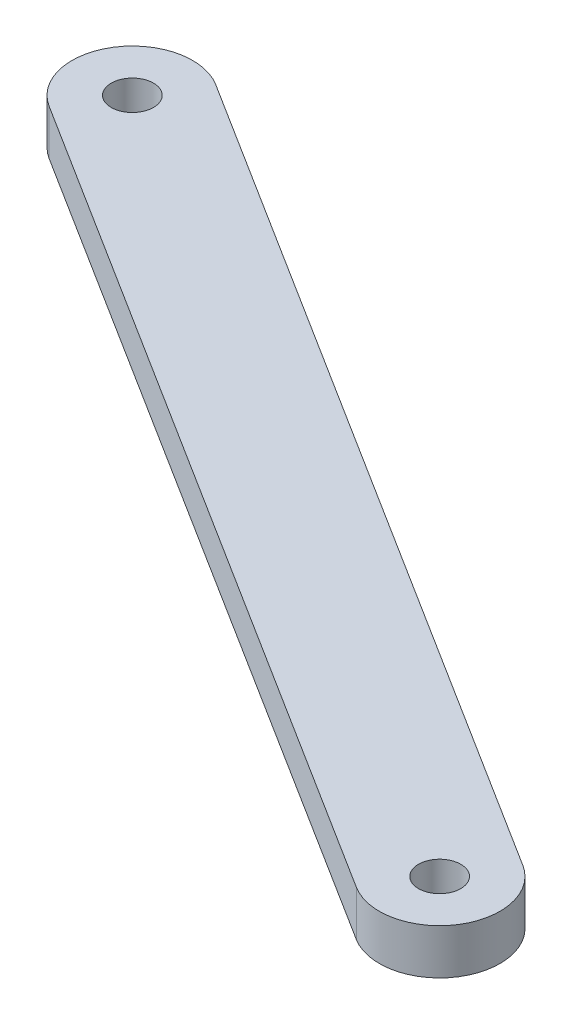
SolidWorks part; units mm, degrees
ref_plane "Front Plane" through (0, 0, 0) normal (0, 0, 1) x (1, 0, 0)
ref_plane "Top Plane" through (0, 0, 0) normal (0, 1, 0) x (1, 0, 0)
ref_plane "Right Plane" through (0, 0, 0) normal (1, 0, 0) x (0, 0, -1)
sketch "Sketch1" plane through (0, 0, 0) normal (0, 1, 0) x (1, 0, 0)
  line L20 (-2.1322, -19.4967) -> (-57.1322, 15.1443)
  line L25 (-61.3957, 8.3751) -> (-6.3957, -26.266)
  circle A59 centre (-4.2639, -22.8813) radius 1.4
  arc A60 (-57.1322, 15.1443) -> (-61.3957, 8.3751) centre (-59.2639, 11.7597) ccw
  arc A61 (-6.3957, -26.266) -> (-2.1322, -19.4967) centre (-4.2639, -22.8813) ccw
  circle A62 centre (-59.2639, 11.7597) radius 1.4
  dimension "D2" = 2.8
  dimension "D1" = 2.8
extrude "Boss-Extrude1" add sketch "Sketch1" along normal blind 3
